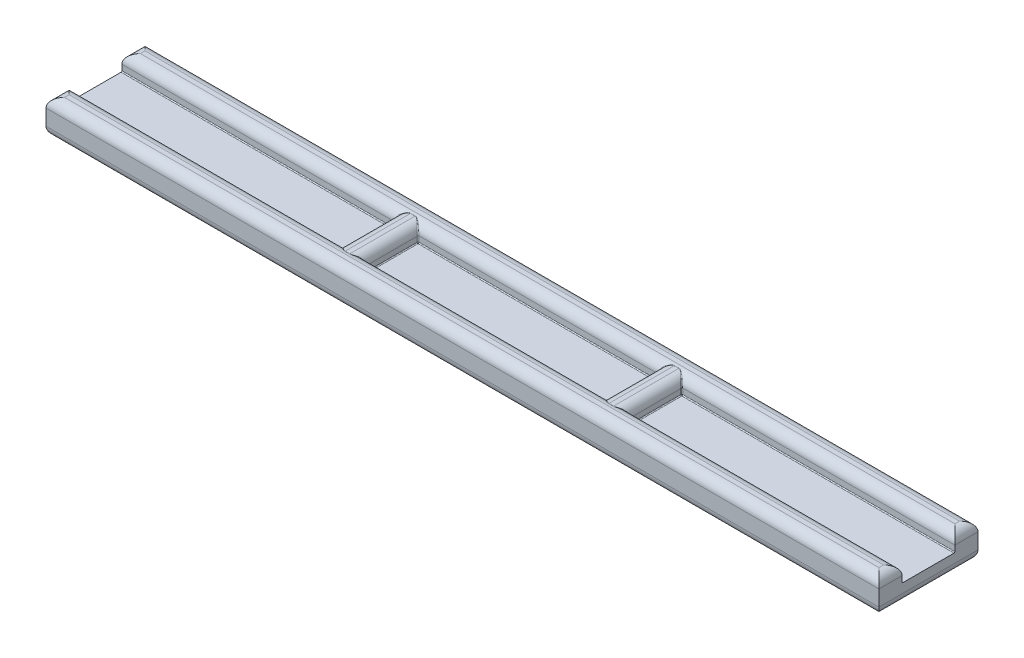
SolidWorks part; units mm, degrees
material "ABS"
ref_plane "Front Plane" through (0, 0, 0) normal (0, 0, 1) x (1, 0, 0)
ref_plane "Top Plane" through (0, 0, 0) normal (0, 1, 0) x (1, 0, 0)
ref_plane "Right Plane" through (0, 0, 0) normal (1, 0, 0) x (0, 0, -1)
sketch "Sketch1" plane through (0, 0, 0) normal (1, 0, 0) x (0, 0, -1)
  line L1 (-5.35, 0) -> (5.35, 0)
  line L10 (-5.35, 0) -> (-5.35, 3.7)
  line L11 (-5.35, 3.7) -> (-2.85, 3.7)
  line L12 (-2.85, 3.7) -> (-2.85, 2)
  line L13 (-2.85, 2) -> (2.85, 2)
  line L14 (2.85, 2) -> (2.85, 3.7)
  line L15 (2.85, 3.7) -> (5.35, 3.7)
  line L16 (5.35, 3.7) -> (5.35, 0)
  point P4 (0, 0)
  dimension "D1" = 10.7
  dimension "D2" = 2.5
  dimension "D3" = 2.5
  dimension "D4" = 2
  dimension "D5" = 3.7
  dimension "D6" = 0
extrude "Boss-Extrude1" add sketch "Sketch1" along normal blind 90
fillet "Fillet1" radius 1 12 edges at (45, 3.7, -5.35) (90, 3.7, -4.1) (45, 3.7, -2.85) (0, 3.7, -4.1) (45, 3.7, 2.85) (90, 3.7, 4.1) (45, 3.7, 5.35) (0, 3.7, 4.1) (45, 0, -5.35) (45, 0, 5.35) (90, 0, 0) (0, 0, 0)
fillet "Fillet2" radius 0.1 2 edges at (45, 2, -2.85) (45, 2, 2.85)
sketch "Sketch2" plane through (0, 0, 0) normal (0, 0, 1) x (1, 0, 0)
  line L0 (0, 1.85) -> (30.75, 1.85) construction
  line L1 (0, 2.7) -> (0, 1) construction
  line L2 (0, 1.85) -> (45, 1.85) construction
  line L3 (45, -16.5673) -> (45, 20.2673) construction
  line L4 (29.5, 2) -> (32, 2)
  line L5 (32, 2) -> (32, 3.65)
  line L6 (32, 3.65) -> (29.5, 3.65)
  line L7 (29.5, 3.65) -> (29.5, 2)
  line L8 (89, 0) -> (1, 0) construction
  point P8 (45, 1.85)
  dimension "D1" = 30.75
  dimension "D2" = 45
  dimension "D3" = 2
  dimension "D4" = 2.5
  dimension "D5" = 1.25
  dimension "D6" = 1.65
extrude "Boss-Extrude2" add sketch "Sketch2" against normal up to surface and the other way up to surface
fillet "Fillet4" radius 1 2 edges at (32, 3.65, 0) (29.5, 3.65, 0)
fillet "Fillet5" radius 0.1 20 edges at (29.5, 2.0293, -2.8207) (29.5, 2.375, -2.85) (29.5003, 2.675, -2.85) (29.8827, 3.4367, -3.1738) (30.75, 3.65, -3.5378) (31.6357, 3.4219, -3.158) (31.9997, 2.675, -2.85) (32, 2.375, -2.85) (32, 2.0293, -2.8207) (32, 2, 0) (32, 2.0293, 2.8207) (32, 2.375, 2.85) (31.9997, 2.675, 2.85) (31.6173, 3.4367, 3.1738) (30.75, 3.65, 3.5378) (29.8643, 3.4219, 3.158) (29.5003, 2.675, 2.85) (29.5, 2.375, 2.85) (29.5, 2.0293, 2.8207) (29.5, 2, 0)
ref_plane "Plane1" through (45, 0, 0) normal (1, 0, 0) x (0, 0, -1)
mirror "Mirror1" about plane through (45, 0, 0) normal (1, 0, 0) of "Fillet5", "Boss-Extrude2", "Fillet4"
